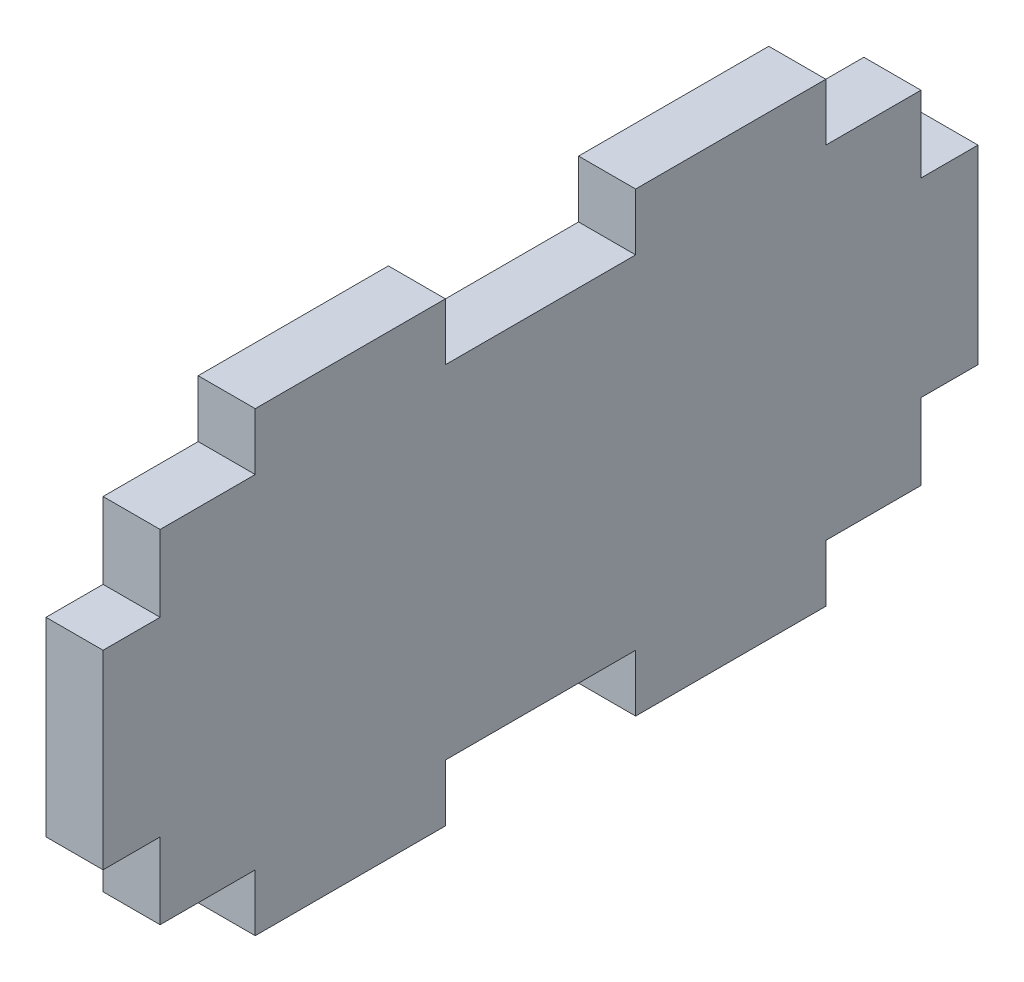
SolidWorks part; units mm, degrees
material "PC High Viscosity"
ref_plane "Front Plane" through (0, 0, 0) normal (0, 0, 1) x (1, 0, 0)
ref_plane "Top Plane" through (0, 0, 0) normal (0, 1, 0) x (1, 0, 0)
ref_plane "Right Plane" through (0, 0, 0) normal (1, 0, 0) x (0, 0, -1)
sketch "Sketch1" plane through (0, 0, 0) normal (1, 0, 0) x (0, 0, -1)
  line L1 (-23, -12) -> (23, -12)
  line L2 (-23, -12) -> (-23, 12)
  line L3 (-23, 12) -> (23, 12)
  line L4 (23, -12) -> (23, 12)
  line L5 (-23, -12) -> (23, 12) construction
  line L6 (-23, 12) -> (23, -12) construction
  point P0 (0, 0)
  dimension "D1" = 46
  dimension "D2" = 24
extrude "Boss-Extrude1" add sketch "Sketch1" along normal blind 3 contours L3 L4 L1 L2
sketch "Sketch2" plane through (3, 0, 0) normal (1, 0, 0) x (0, 0, -1)
  line L0 (23, -12) -> (23, 12) construction
  line L1 (23, 5) -> (20, 5)
  line L2 (23, 5) -> (23, -5) construction
  line L3 (23, -5) -> (20, -5) construction
  line L4 (20, 5) -> (20, -5) construction
  line L5 (0, 0) -> (23, 0) construction
  line L6 (20, 5) -> (20, 9)
  line L7 (20, 9) -> (15, 9)
  line L8 (15, 9) -> (15, 12)
  line L9 (-23, 12) -> (23, 12) construction
  line L10 (15, 12) -> (23, 12)
  line L11 (23, 12) -> (23, 5)
  line L13 (0, 12) -> (5, 12)
  line L14 (0, 12) -> (0, 9)
  line L15 (0, 9) -> (5, 9)
  line L16 (5, 12) -> (5, 9)
  dimension "D1" = 10
  dimension "D2" = 3
  dimension "D3" = 8
  dimension "D4" = 5
extrude "Cut-Extrude1" cut sketch "Sketch2" against normal through all
mirror "Mirror1" about plane through (0, 0, 0) normal (0, 1, 0) of "Cut-Extrude1"
mirror "Mirror2" about plane through (0, 0, 0) normal (0, 0, 1) of "Mirror1", "Cut-Extrude1"
equation "\"pulley_pitch_diam\"= 12.73mm"
equation "\"pulley_total_width\"= 16mm"
equation "\"pulley_total_diam\"= 16mm"
equation "\"belt_width\"= 6mm"
equation "\"material_thickness\"= 3mm"
equation "\"shaft_diam\"= 8mm"
equation "\"bearing_od\"= 22mm"
equation "\"bearing_thickness\"= 7mm"
equation "\"D1@Boss-Extrude1\"=\"material_thickness\""
equation "\"D2@Sketch2\"=\"material_thickness\""
